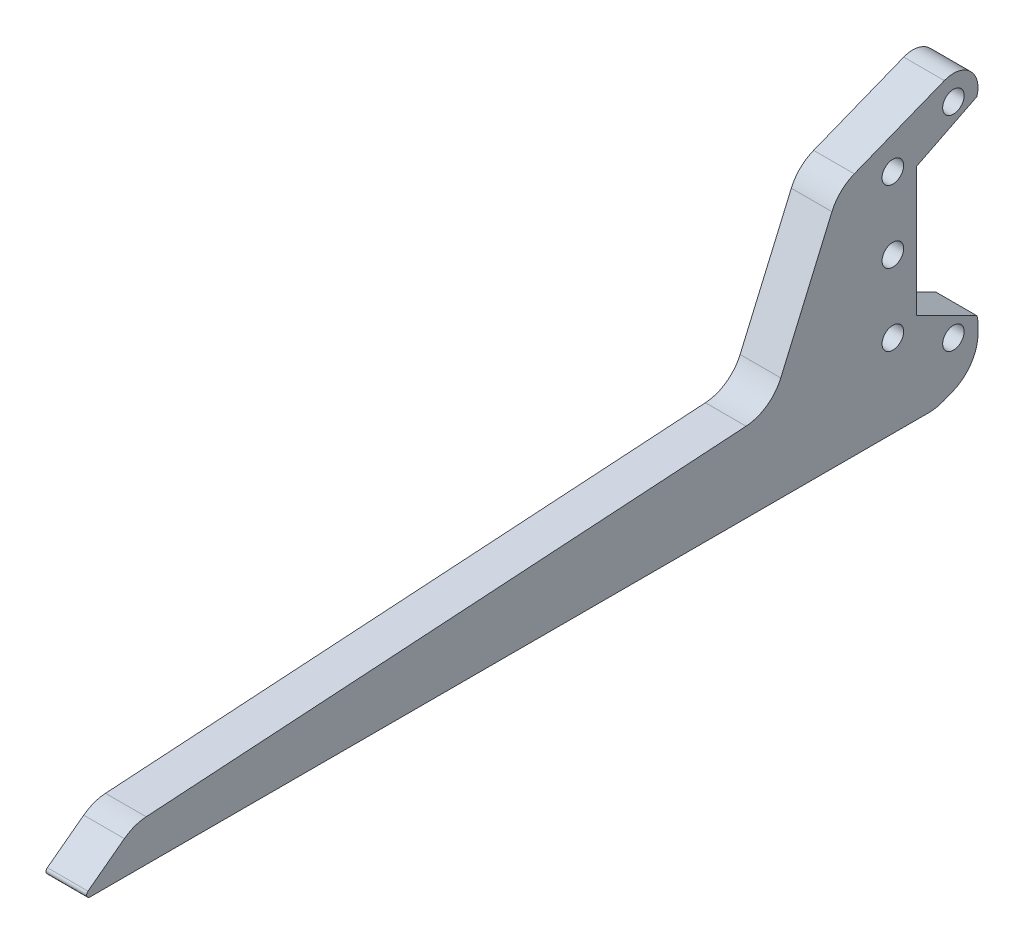
SolidWorks part; units mm, degrees
material "Plain Carbon Steel"
ref_plane "Front Plane" through (0, 0, 0) normal (0, 0, 1) x (1, 0, 0)
ref_plane "Top Plane" through (0, 0, 0) normal (0, 1, 0) x (1, 0, 0)
ref_plane "Right Plane" through (0, 0, 0) normal (1, 0, 0) x (0, 0, -1)
sketch "Sketch1" plane through (0, 0, 0) normal (1, 0, 0) x (0, 0, -1)
  line L0 (-160.655, 50.8) -> (93.345, 50.8)
  line L1 (93.345, 50.8) -> (93.345, -50.8)
  line L2 (93.345, -50.8) -> (-160.655, -50.8)
  line L3 (93.345, 0) -> (55.245, 50.8)
  line L4 (93.345, 0) -> (55.245, -50.8)
  circle A0 centre (0, 0) radius 38.1
  circle A1 centre (0, 0) radius 7.9375
  circle A2 centre (-38.1, 0) radius 7.9375
  circle A3 centre (-88.9, 0) radius 7.9375
  circle A4 centre (-88.9, 0) radius 39.751
  circle A5 centre (-38.1, 0) radius 25.4
  circle A6 centre (-160.655, 0) radius 11.1125
  circle A7 centre (-88.9, 0) radius 23.368
  circle A8 centre (-160.655, 0) radius 33.655
  circle A9 centre (-160.655, 0) radius 76.2
  circle A10 centre (-160.655, 0) radius 50.8
  dimension "D1" = 38.1
  dimension "D3" = 71.755
  dimension "D4" = 15.875
  dimension "D5" = 101.6
  dimension "D9" = 50.8
  dimension "D10" = 67.31
  dimension "D11" = 79.502
  dimension "D12" = 46.736
  dimension "D2" = 50.8
  dimension "D6" = 254
  dimension "D7" = 38.1
  dimension "D8" = 38.1
extrude "Boss-Extrude1" add sketch "Sketch1" along normal blind 12.7 contours A5 A0 A1 | A0 A5 | A10 A7 A9 A3 | A10 A7 A9 A4 | A7 A10 A4 | A7 A10 | A10 A4 A9 A7 | A9 A4 A5 A7 | A10 L2 A9 A4 | A4 A10 A8 | A8 A6 | A10 A4 A9 L0 | A9 A4 A5 A0 L2 L4 L3 L0 | A9 A3 A7 | A4 A5 | A0 A5 A4 A2 | A4 A8
hole_wizard "#8 Clearance Hole1" positions "Sketch3" profile "Sketch4" hole size "#8" standard "ANSI Inch" end condition through all
sketch "Sketch3" plane through (0, 0, 0) normal (-1, 0, 0) x (0, 0, 1)
  point P0 (-17.6911, 17.6911)
  point P3 (17.6911, 17.6911)
  point P6 (17.6911, -17.6911)
  point P9 (-17.6911, -17.6911)
sketch "Sketch4" plane through (0, 17.6911, -17.6911) normal (0, 1, 0) x (0, 0, 1)
  line L0 (0, 0) -> (0, 12.7)
  line L1 (0, 12.7) -> (2.2479, 12.7)
  line L2 (2.2479, 12.7) -> (2.2479, 0)
  line L5 (2.2479, 0) -> (0, 0)
  line L11 (0, -6.35) -> (0, 107.95) construction
  dimension "Thru Hole Dia." = 4.4958
  dimension "Thru Hole Depth" = 12.7
sketch "Sketch5" plane through (0, 0, 0) normal (-1, 0, 0) x (0, 0, 1)
  circle A0 centre (0, 0) radius 18.415
extrude "Cut-Extrude1" cut sketch "Sketch5" against normal through all
sketch "Sketch7" plane through (0, 0, 0) normal (-1, 0, 0) x (0, 0, 1)
  circle A0 centre (-55.245, 0) radius 9.525
  dimension "D1" = 38.1
extrude "Cut-Extrude2" cut sketch "Sketch7" against normal through all
sketch "Sketch8" plane through (12.7, 0, 0) normal (1, 0, 0) x (0, 0, -1)
  line L0 (-160.655, 50.8) -> (-211.455, 25.4)
  line L1 (-211.455, 25.4) -> (-211.455, -25.4)
  line L2 (-211.455, -25.4) -> (-160.655, -50.8)
  line L3 (-160.655, -50.8) -> (-233.2397, -50.8)
  line L4 (-233.2397, -50.8) -> (-233.2397, 50.8)
  line L5 (-233.2397, 50.8) -> (-160.655, 50.8)
  line L6 (-211.455, 0) -> (-160.655, 0) construction
  arc A0 (-160.655, 50.8) -> (-160.655, -50.8) centre (-160.655, 0) ccw construction
  dimension "D1" = 50.8
extrude "Cut-Extrude3" cut sketch "Sketch8" against normal through all
sketch "Sketch9" plane through (12.7, 0, 0) normal (1, 0, 0) x (0, 0, -1)
  line L0 (-160.655, 50.8) -> (-211.455, 25.4)
  line L1 (-211.455, 25.4) -> (-211.455, 0)
  line L2 (-211.455, 0) -> (-211.455, -25.4)
  line L3 (-211.455, -25.4) -> (-160.655, -50.8)
  line L4 (-160.655, -50.8) -> (-160.655, -40.64)
  line L5 (-160.655, -40.64) -> (-202.7493, 0)
  line L6 (-202.7493, 0) -> (-160.655, 40.64)
  line L7 (-160.655, 40.64) -> (-160.655, 50.8)
  line L8 (-160.655, -50.8) -> (-201.295, -30.48) construction
  line L9 (-201.295, 30.48) -> (-160.655, 50.8) construction
  arc A0 (-201.295, 30.48) -> (-201.295, -30.48) centre (-160.655, 0) ccw construction
extrude "Boss-Extrude2" add sketch "Sketch9" against normal blind 12.7
sketch "Sketch10" plane through (0, 0, 0) normal (-1, 0, 0) x (0, 0, 1)
  line L0 (-79.0575, -19.05) -> (-79.0575, 19.05)
  line L1 (-93.345, 0) -> (-55.245, -50.8) construction
  line L3 (-93.345, 0) -> (-55.245, 50.8) construction
  line L4 (-79.0575, 19.05) -> (-93.345, 0)
  line L5 (-93.345, 0) -> (-79.0575, -19.05)
extrude "Cut-Extrude4" cut sketch "Sketch10" against normal through all
sketch "Sketch11" plane through (0, 50.8, 0) normal (0, 1, 0) x (1, 0, 0)
  line L0 (0, -160.655) -> (0, 55.245) construction
  line L1 (0, 36.322) -> (12.7, 36.322)
  line L2 (0, 36.322) -> (0, -141.732)
  line L3 (0, -141.732) -> (12.7, -141.732)
  line L4 (12.7, 36.322) -> (12.7, -141.732)
  line L5 (12.7, -160.655) -> (12.7, 55.245) construction
  line L6 (12.7, -141.605) -> (0, -141.605) construction
  line L7 (0, 36.195) -> (12.7, 36.195) construction
  dimension "D1" = 0.127
  dimension "D2" = 0.127
extrude "Cut-Extrude5" cut sketch "Sketch11" against normal blind 3.175
mirror "Mirror1" about plane through (0, 0, 0) normal (0, 1, 0) of "Cut-Extrude5"
sketch "Sketch12" plane through (12.7, 0, 0) normal (1, 0, 0) x (0, 0, -1)
  line L16 (-162.154, 57.15) -> (-166.9165, 66.675)
  line L17 (-166.9165, 66.675) -> (-185.9665, 66.675)
  line L18 (-185.9665, 66.675) -> (-243.205, 43.9892)
  line L19 (-243.205, 43.9892) -> (-243.205, -43.9892)
  line L20 (-243.205, -43.9892) -> (-185.9665, -66.675)
  line L21 (-185.9665, -66.675) -> (-166.9165, -66.675)
  line L22 (-166.9165, -66.675) -> (-162.154, -57.15)
  line L23 (-243.205, 43.9892) -> (-217.805, 29.3245) construction
  line L24 (-217.805, -29.3245) -> (-243.205, -43.9892) construction
  line L32 (-162.154, -57.15) -> (-135.382, -57.15)
  line L33 (-135.382, -57.15) -> (-135.382, -53.975)
  line L34 (-135.382, -53.975) -> (29.972, -53.975)
  line L35 (29.972, -53.975) -> (29.972, -57.15)
  line L36 (29.972, -57.15) -> (58.42, -57.15)
  line L37 (58.42, -57.15) -> (85.4075, -21.1667)
  line L38 (85.4075, -21.1667) -> (85.4075, 21.1667)
  line L39 (85.4075, 21.1667) -> (58.42, 57.15)
  line L40 (58.42, 57.15) -> (29.972, 57.15)
  line L41 (29.972, 57.15) -> (29.972, 53.975)
  line L42 (29.972, 53.975) -> (-135.382, 53.975)
  line L43 (-135.382, 53.975) -> (-135.382, 57.15)
  line L44 (-135.382, 57.15) -> (-162.154, 57.15)
  line L45 (-162.154, 57.15) -> (-217.805, 29.3245)
  line L46 (-217.805, 29.3245) -> (-217.805, -29.3245)
  line L47 (-217.805, -29.3245) -> (-162.154, -57.15)
  line L48 (-162.154, -57.15) -> (-135.382, -57.15)
  line L49 (-135.382, -57.15) -> (-135.382, -53.975)
  line L50 (-135.382, -53.975) -> (29.972, -53.975)
  line L51 (29.972, -53.975) -> (29.972, -57.15)
  line L52 (29.972, -57.15) -> (58.42, -57.15)
  line L53 (58.42, -57.15) -> (85.4075, -21.1667)
  line L54 (85.4075, -21.1667) -> (85.4075, 21.1667)
  line L55 (85.4075, 21.1667) -> (58.42, 57.15)
  line L56 (58.42, 57.15) -> (29.972, 57.15)
  line L57 (29.972, 57.15) -> (29.972, 53.975)
  line L58 (29.972, 53.975) -> (-135.382, 53.975)
  line L59 (-135.382, 53.975) -> (-135.382, 57.15)
  line L60 (-135.382, 57.15) -> (-162.154, 57.15)
  line L61 (-162.154, 57.15) -> (-217.805, 29.3245)
  line L62 (-217.805, 29.3245) -> (-217.805, -29.3245)
  line L63 (-217.805, -29.3245) -> (-162.154, -57.15)
  circle A0 centre (-160.655, 0) radius 76.2
  dimension "D2" = 9.525
  dimension "D3" = 9.525
  dimension "D4" = 25.4
  dimension "D5" = 120
  dimension "D6" = 120
  dimension "D7" = 19.05
  dimension "D8" = 19.05
  dimension "D1" = 6.35
extrude "Boss-Extrude3" add sketch "Sketch12" against normal blind 19.05 separate body contours A0 L18 L19 L20 | L18 A0 L20 L21 L22 L63 L62 L61 L16 L17
sketch "Sketch13" plane through (12.7, 0, 0) normal (1, 0, 0) x (0, 0, -1)
  line L32 (-161.2546, -53.34) -> (-139.192, -53.34)
  line L33 (-139.192, -53.34) -> (-139.192, -50.165)
  line L34 (-139.192, -50.165) -> (33.782, -50.165)
  line L35 (33.782, -50.165) -> (33.782, -53.34)
  line L36 (33.782, -53.34) -> (56.515, -53.34)
  line L37 (56.515, -53.34) -> (81.5975, -19.8967)
  line L38 (81.5975, -19.8967) -> (81.5975, 19.8967)
  line L39 (81.5975, 19.8967) -> (56.515, 53.34)
  line L40 (56.515, 53.34) -> (33.782, 53.34)
  line L41 (33.782, 53.34) -> (33.782, 50.165)
  line L42 (33.782, 50.165) -> (-139.192, 50.165)
  line L43 (-139.192, 50.165) -> (-139.192, 53.34)
  line L44 (-139.192, 53.34) -> (-161.2546, 53.34)
  line L45 (-161.2546, 53.34) -> (-213.995, 26.9698)
  line L46 (-213.995, 26.9698) -> (-213.995, -26.9698)
  line L47 (-213.995, -26.9698) -> (-161.2546, -53.34)
  line L48 (-161.2546, -53.34) -> (-139.192, -53.34)
  line L49 (-139.192, -53.34) -> (-139.192, -50.165)
  line L50 (-139.192, -50.165) -> (33.782, -50.165)
  line L51 (33.782, -50.165) -> (33.782, -53.34)
  line L52 (33.782, -53.34) -> (56.515, -53.34)
  line L53 (56.515, -53.34) -> (81.5975, -19.8967)
  line L54 (81.5975, -19.8967) -> (81.5975, 19.8967)
  line L55 (81.5975, 19.8967) -> (56.515, 53.34)
  line L56 (56.515, 53.34) -> (33.782, 53.34)
  line L57 (33.782, 53.34) -> (33.782, 50.165)
  line L58 (33.782, 50.165) -> (-139.192, 50.165)
  line L59 (-139.192, 50.165) -> (-139.192, 53.34)
  line L60 (-139.192, 53.34) -> (-161.2546, 53.34)
  line L61 (-161.2546, 53.34) -> (-213.995, 26.9698)
  line L62 (-213.995, 26.9698) -> (-213.995, -26.9698)
  line L63 (-213.995, -26.9698) -> (-161.2546, -53.34)
  dimension "D1" = 2.54
extrude "Cut-Extrude6" cut sketch "Sketch13" against normal through all
hole_wizard "3/8 Clearance Hole1" positions "Sketch15" profile "Sketch14" hole size "3/8" standard "ANSI Inch" end condition through all
sketch "Sketch15" plane through (12.7, 0, 0) normal (1, 0, 0) x (0, 0, -1)
  line L0 (-185.9665, -66.675) -> (-177.394, -49.53) construction
  line L1 (-217.805, -29.3245) -> (-162.154, -57.15) construction
  line L3 (-230.505, 49.0227) -> (-230.505, -49.0227) construction
  line L4 (-185.9665, 66.675) -> (-243.205, 43.9892) construction
  line L5 (-243.205, -43.9892) -> (-185.9665, -66.675) construction
  line L11 (-243.205, 0) -> (-230.505, 0) construction
  line L12 (-243.205, 43.9892) -> (-243.205, -43.9892) construction
  line L13 (-230.505, 0) -> (-217.805, 0) construction
  line L14 (-217.805, 29.3245) -> (-217.805, -29.3245) construction
  line L16 (-181.6803, -58.1025) -> (-230.505, -33.6901) construction
  line L18 (-185.9665, 66.675) -> (-177.394, 49.53) construction
  line L19 (-162.154, 57.15) -> (-217.805, 29.3245) construction
  line L23 (-230.505, 33.6901) -> (-181.6803, 58.1025) construction
  point P0 (-230.505, 0)
  point P2 (-230.505, 33.6901)
  point P4 (-202.1069, 47.8892)
  point P6 (-230.505, -33.6901)
  point P8 (-202.1069, -47.8892)
  dimension "D1" = 31.75
sketch "Sketch14" plane through (12.7, 0, 230.505) normal (0, 1, 0) x (0, 0, -1)
  line L0 (0, 0) -> (0, 19.05)
  line L1 (0, 19.05) -> (5.0419, 19.05)
  line L2 (5.0419, 19.05) -> (5.0419, 0)
  line L5 (5.0419, 0) -> (0, 0)
  line L11 (0, -6.35) -> (0, 107.95) construction
  dimension "Thru Hole Dia." = 10.0838
  dimension "Thru Hole Depth" = 19.05
sketch "Sketch16" plane through (12.7, 0, 0) normal (1, 0, 0) x (0, 0, -1)
  line L16 (-230.505, 0) -> (-132.2223, 0) construction
  line L17 (-132.2223, 0) -> (-132.2223, -76.2) construction
  line L18 (-132.2223, -76.2) -> (-544.0497, -76.2) construction
  line L19 (-219.3925, -30.3056) -> (-162.864, -58.5699)
  line L20 (-219.3925, 30.3056) -> (-219.3925, -30.3056)
  line L21 (-162.864, 58.5699) -> (-219.3925, 30.3056)
  line L22 (-219.3925, -30.3056) -> (-162.864, -58.5699)
  line L23 (-219.3925, 30.3056) -> (-219.3925, -30.3056)
  line L24 (-162.864, 58.5699) -> (-219.3925, 30.3056)
  line L25 (-190.5898, -47.8892) -> (-190.5898, -66.675)
  line L26 (-190.5898, -66.675) -> (-155.601, -66.675)
  line L27 (-155.601, -66.675) -> (-155.601, 66.675)
  line L28 (-155.601, 66.675) -> (-185.9665, 66.675)
  line L29 (-185.9665, 66.675) -> (-206.3505, 58.5961)
  line L30 (-202.1069, 36.372) -> (-202.1069, -36.372)
  circle A0 centre (-202.1069, 47.8892) radius 11.5172
  circle A1 centre (-202.1069, -47.8892) radius 11.5172
  line M9 (-243.205, -43.9892) -> (-185.9665, -66.675)
  line M10 (-185.9665, -66.675) -> (-166.9165, -66.675)
  line M11 (-166.9165, -66.675) -> (-162.154, -57.15)
  line M12 (-162.154, -57.15) -> (-217.805, -29.3245)
  line M13 (-217.805, -29.3245) -> (-217.805, 29.3245)
  line M14 (-217.805, 29.3245) -> (-162.154, 57.15)
  line M15 (-162.154, 57.15) -> (-166.9165, 66.675)
  line M16 (-166.9165, 66.675) -> (-185.9665, 66.675)
  line M17 (-185.9665, 66.675) -> (-243.205, 43.9892)
  dimension "D2" = 76.2
  dimension "D1" = 1.5875
extrude "Cut-Extrude7" cut sketch "Sketch16" against normal through all contours A0 L24 M15 M16 M17 | A0 L24 M14 M15 | L24 A0 M14 | A1 A0 L24 L23 L22 M12 M13 M14 | L22 A1 M12 | A1 L22 M11 M12 | A1 L25 L22 M9 M10 M11
sketch "Sketch17" plane through (12.7, 0, 0) normal (1, 0, 0) x (0, 0, -1)
  line L0 (-230.505, 0) -> (-230.505, -72.5642) construction
  line L1 (-230.505, -72.5642) -> (-382.905, -72.5642) construction
  line L2 (-490.855, -72.5642) -> (-210.0721, -72.5642)
  line L3 (-210.0721, -72.5642) -> (-190.5898, -64.8426)
  line L4 (-190.5898, -64.8426) -> (-243.205, -43.9892)
  line L5 (-243.205, -43.9892) -> (-243.205, 43.9892)
  line L6 (-243.205, 43.9892) -> (-255.905, 38.9557)
  line L7 (-255.905, 38.9557) -> (-287.655, -34.4642)
  line L8 (-490.855, -72.5642) -> (-497.205, -72.5642)
  line L9 (-586.105, -53.5142) -> (-287.655, -34.4642)
  line L10 (-497.205, -72.5642) -> (-611.505, -72.5642)
  line L11 (-611.505, -72.5642) -> (-586.105, -53.5142)
  line L18 (-206.3505, 58.5961) -> (-243.205, 43.9892) construction
  circle A0 centre (-230.505, -33.6901) radius 5.0419 construction
  circle A1 centre (-230.505, 33.6901) radius 5.0419 construction
  dimension "D2" = 38.1
  dimension "D3" = 203.2
  dimension "D4" = 19.05
  dimension "D5" = 28.575
  dimension "D6" = 57.15
  dimension "D7" = 25.4
  dimension "D9" = 25.4
  dimension "D10" = 381
extrude "Boss-Extrude4" add sketch "Sketch17" against normal blind 19.05
fillet "Fillet1" radius 19.05 5 edges at (3.175, -64.8426, 190.5898) (3.175, -72.5642, 210.0721) (3.175, 38.9557, 255.905) (3.175, -34.4642, 287.655) (3.175, -53.5142, 586.105)
fillet "Fillet3" radius 1.5875 1 edges at (3.175, -72.5642, 611.505)
